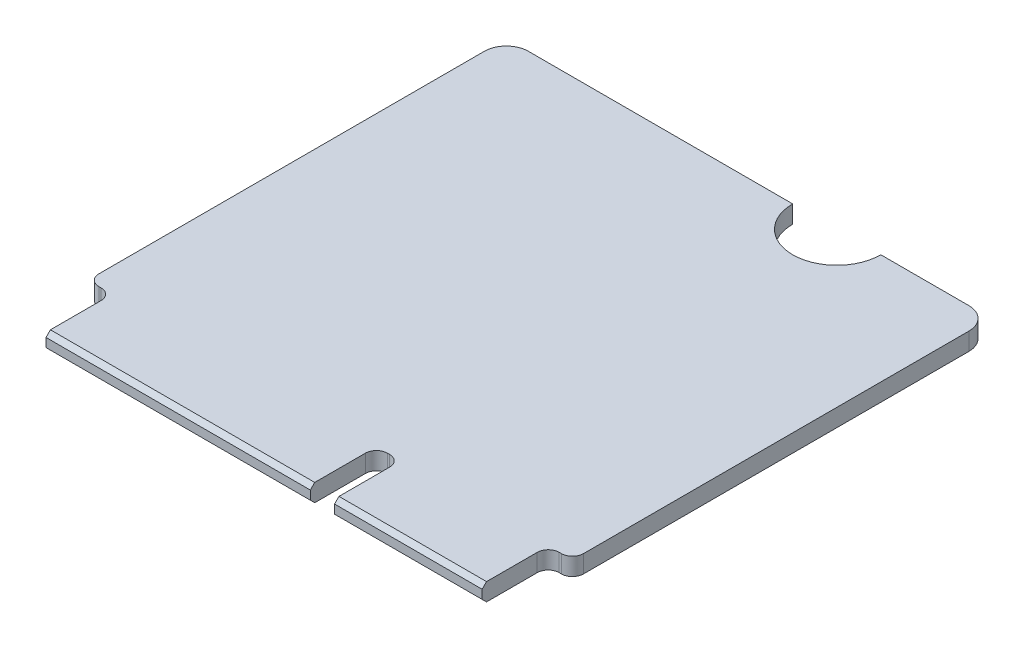
SolidWorks part; units mm, degrees
ref_plane "Front Plane" through (0, 0, 0) normal (0, 0, 1) x (1, 0, 0)
ref_plane "Top Plane" through (0, 0, 0) normal (0, 1, 0) x (1, 0, 0)
ref_plane "Right Plane" through (0, 0, 0) normal (1, 0, 0) x (0, 0, -1)
sketch "Sketch1" plane through (0, 0, 0) normal (0, 1, 0) x (1, 0, 0)
  line L0 (14.2, -22) -> (20.9, -22)
  line L1 (0, 0) -> (13, 0)
  line L2 (0, 0) -> (0, -19)
  line L3 (1.1, -22) -> (13.1, -22)
  line L4 (22, 0) -> (22, -19)
  line L6 (13.1, -22) -> (13.1, -19)
  line L7 (13.1, -19) -> (14.2, -19)
  line L8 (14.2, -22) -> (14.2, -19)
  line L9 (17, 0) -> (22, 0)
  line L10 (0, -19) -> (1.1, -19)
  line L13 (1.1, -19) -> (1.1, -22)
  line L14 (22, -19) -> (20.9, -19)
  line L17 (20.9, -19) -> (20.9, -22)
  arc A0 (13, 0) -> (17, 0) centre (15, 0) ccw
  dimension "D6" = 2
  dimension "D1" = 22
  dimension "D2" = 22
  dimension "D4" = 3
  dimension "D5" = 15
  dimension "D7" = 6.7
  dimension "D8" = 12
extrude "Boss-Extrude1" add sketch "Sketch1" along normal blind 0.8
fillet "Fillet1" radius 1 2 edges at (22, 0.4, 0) (0, 0.4, 0)
fillet "Fillet2" radius 0.5 6 edges at (0, 0.4, 19) (1.1, 0.4, 19) (14.2, 0.4, 19) (13.1, 0.4, 19) (22, 0.4, 19) (20.9, 0.4, 19)
chamfer "Chamfer1" distance 0.2 angle 45 4 edges at (17.55, 0, 22) (17.55, 0.8, 22) (7.1, 0, 22) (7.1, 0.8, 22)
